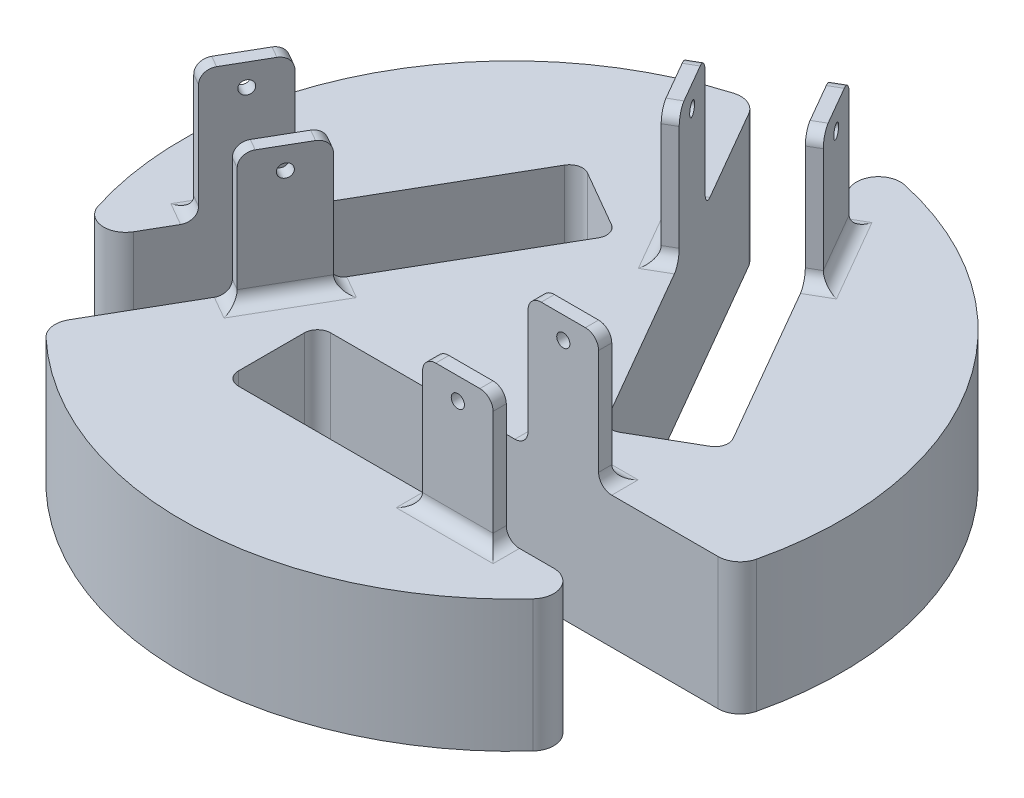
SolidWorks part; units mm, degrees
material "ABS"
ref_plane "Front Plane" through (0, 0, 0) normal (0, 0, 1) x (1, 0, 0)
ref_plane "Top Plane" through (0, 0, 0) normal (0, 1, 0) x (1, 0, 0)
ref_plane "Right Plane" through (0, 0, 0) normal (1, 0, 0) x (0, 0, -1)
sketch "Sketch1" plane through (0, 0, 0) normal (0, 1, 0) x (1, 0, 0)
  circle A0 centre (0, 0) radius 75
  dimension "D1" = 150
extrude "Boss-Extrude1" add sketch "Sketch1" along normal blind 30
sketch "Sketch2" plane through (0, 30, 0) normal (0, 1, 0) x (1, 0, 0)
  line L0 (0, 63.3881) -> (-54.8957, -31.694) construction
  line L1 (-54.8957, -31.694) -> (54.8957, -31.694) construction
  line L2 (54.8957, -31.694) -> (0, 63.3881) construction
  line L3 (0, 63.3881) -> (0, -31.694) construction
  line L4 (-54.8957, -31.694) -> (27.4478, 15.847) construction
  line L5 (54.8957, -31.694) -> (-27.4478, 15.847) construction
  line L6 (3.3338, 30.6137) -> (26.7165, 44.1137)
  line L7 (40.8957, -45.194) -> (24.8454, -45.194)
  line L8 (40.8957, -45.194) -> (40.8957, -18.194)
  line L9 (40.8957, -18.194) -> (24.8454, -18.194)
  line L10 (24.8454, -45.194) -> (24.8454, -18.194)
  line L11 (40.8957, -45.194) -> (24.8454, -18.194) construction
  line L12 (40.8957, -18.194) -> (24.8454, -45.194) construction
  line L13 (-59.587, -12.8197) -> (-36.2044, -26.3197)
  line L14 (-59.587, -12.8197) -> (-51.5619, 1.0803)
  line L15 (-51.5619, 1.0803) -> (-28.1792, -12.4197)
  line L16 (-36.2044, -26.3197) -> (-28.1792, -12.4197)
  line L17 (-59.587, -12.8197) -> (-28.1792, -12.4197) construction
  line L18 (-51.5619, 1.0803) -> (-36.2044, -26.3197) construction
  line L19 (3.3338, 30.6137) -> (-4.6913, 44.5137)
  line L20 (-4.6913, 44.5137) -> (18.6913, 58.0137)
  line L21 (26.7165, 44.1137) -> (18.6913, 58.0137)
  line L22 (3.3338, 30.6137) -> (18.6913, 58.0137) construction
  line L23 (-4.6913, 44.5137) -> (26.7165, 44.1137) construction
  line L24 (-55.5745, -5.8697) -> (-32.1918, -19.3697) construction
  line L25 (32.8705, -18.194) -> (32.8705, -45.194) construction
  line L26 (-32.1918, -19.3697) -> (32.8705, -45.194) construction
  line L27 (22.7039, 51.0637) -> (-0.6788, 37.5637) construction
  line L28 (-0.6788, 37.5637) -> (-55.5745, -5.8697) construction
  line L29 (32.8705, -18.194) -> (22.7039, 51.0637) construction
  point P3 (0, 0)
  point P7 (-43.8831, -12.6197)
  point P10 (32.8705, -31.694)
  point P18 (11.0126, 44.3137)
  dimension "D1" = 14
  dimension "D2" = 27
  dimension "D3" = 27
  dimension "D4" = 27
  dimension "D5" = 70
  dimension "D6" = 14
  dimension "D7" = 14
  dimension "D8" = 70
  dimension "D9" = 70
  dimension "D10" = 95.0821
extrude "Boss-Extrude3" add sketch "Sketch2" along normal blind 30
ref_plane "Plane1" through (24.8454, 30, 18.194) normal (0, 0, 1) x (1, 0, 0)
sketch "Sketch3" plane through (24.8454, 30, 18.194) normal (0, 0, 1) x (1, 0, 0)
  line L0 (16.0503, 25) -> (0, 25) construction
  line L1 (16.0503, 30) -> (16.0503, 0) construction
  line L2 (0, 30) -> (0, 0) construction
  line L3 (8.0252, 25) -> (8.0252, 30) construction
  line L4 (16.0503, 30) -> (0, 30) construction
  circle A0 centre (8.0252, 25) radius 1.5
  dimension "D1" = 3
  dimension "D2" = 5
extrude "Cut-Extrude3" cut sketch "Sketch3" against normal through all both and the other way through all
sketch "Sketch4" plane through (-39.1392, 0, -22.597) normal (-0.866, 0, -0.5) x (-0.5, 0, 0.866)
  line L0 (24.8454, 55) -> (40.8957, 55) construction
  line L2 (40.8957, 60) -> (40.8957, 30) construction
  line L4 (32.8705, 55) -> (32.8705, 60) construction
  line L5 (24.8454, 60) -> (40.8957, 60) construction
  circle A0 centre (32.8705, 55) radius 1.5
  point P9 (24.8454, 55)
  point P10 (40.8957, 55)
  dimension "D1" = 3
  dimension "D2" = 5
extrude "Cut-Extrude4" cut sketch "Sketch4" against normal through all
sketch "Sketch6" plane through (39.1392, 0, -22.597) normal (0.866, 0, -0.5) x (-0.5, 0, -0.866)
  line L0 (24.8454, 55) -> (40.8957, 55) construction
  line L1 (24.8454, 60) -> (24.8454, 30) construction
  line L2 (40.8957, 60) -> (40.8957, 30) construction
  line L3 (32.8705, 55) -> (32.8705, 60) construction
  line L4 (24.8454, 60) -> (40.8957, 60) construction
  circle A0 centre (32.8705, 55) radius 1.5
  dimension "D1" = 3
  dimension "D2" = 5
extrude "Cut-Extrude5" cut sketch "Sketch6" against normal through all
sketch "Sketch7" plane through (0, 60, 0) normal (0, 1, 0) x (1, 0, 0)
  line L0 (40.8957, -42.194) -> (40.8957, -21.194)
  line L1 (40.8957, -42.194) -> (24.845, -42.194)
  line L2 (40.8957, -21.194) -> (24.845, -21.194)
  line L3 (24.845, -42.194) -> (24.845, -21.194)
  line L4 (40.8957, -45.194) -> (40.8957, -18.194) construction
  line L5 (32.8703, -42.194) -> (32.8705, -45.194) construction
  line L8 (24.8454, -45.194) -> (40.8957, -45.194) construction
  line L9 (32.8703, -21.194) -> (32.8705, -18.194) construction
  line L10 (40.8957, -18.194) -> (24.8454, -18.194) construction
  dimension "D1" = 21
  dimension "D2" = 3
  dimension "D3" = 3
extrude "Cut-Extrude6" cut sketch "Sketch7" against normal blind 24
sketch "Sketch8" plane through (0, 60, 0) normal (0, 1, 0) x (1, 0, 0)
  line L0 (-30.7773, -10.9197) -> (-48.9638, -0.4197)
  line L1 (-30.7773, -10.9197) -> (-38.8024, -24.8197)
  line L2 (-48.9638, -0.4197) -> (-56.989, -14.3197)
  line L3 (-38.8024, -24.8197) -> (-56.989, -14.3197)
  line L4 (-28.1792, -12.4197) -> (-51.5619, 1.0803) construction
  line L6 (-59.587, -12.8197) -> (-36.2044, -26.3197) construction
  line L7 (-34.7898, -17.8697) -> (-32.1918, -19.3697) construction
  line L8 (-36.2044, -26.3197) -> (-28.1792, -12.4197) construction
  line L9 (-52.9764, -7.3697) -> (-55.5745, -5.8697) construction
  line L10 (-51.5619, 1.0803) -> (-59.587, -12.8197) construction
  dimension "D1" = 21
extrude "Cut-Extrude7" cut sketch "Sketch8" against normal blind 24
sketch "Sketch9" plane through (0, 60, 0) normal (0, 1, 0) x (1, 0, 0)
  line L0 (16.0933, 56.5137) -> (24.1184, 42.6137)
  line L1 (16.0933, 56.5137) -> (-2.0933, 46.0137)
  line L2 (24.1184, 42.6137) -> (5.9319, 32.1137)
  line L3 (-2.0933, 46.0137) -> (5.9319, 32.1137)
  line L4 (18.6913, 58.0137) -> (-4.6913, 44.5137) construction
  line L5 (3.3338, 30.6137) -> (26.7165, 44.1137) construction
  line L6 (1.9193, 39.0637) -> (-0.6788, 37.5637) construction
  line L7 (-4.6913, 44.5137) -> (3.3338, 30.6137) construction
  line L8 (20.1059, 49.5637) -> (22.7039, 51.0637) construction
  line L9 (26.7165, 44.1137) -> (18.6913, 58.0137) construction
  dimension "D1" = 21
extrude "Cut-Extrude8" cut sketch "Sketch9" against normal blind 24
fillet "Fillet4" radius 3 12 edges at (-0.6788, 30, -37.5637) (15.0252, 30, -37.3637) (7, 30, -51.2637) (22.7039, 30, -51.0637) (32.8705, 30, 18.194) (40.8957, 30, 31.694) (32.8705, 30, 45.194) (24.8454, 30, 31.694) (-32.1918, 30, 19.3697) (-47.8957, 30, 19.5697) (-39.8705, 30, 5.6697) (-55.5745, 30, 5.8697)
sketch "Sketch10" plane through (0, 36, 0) normal (0, 1, 0) x (1, 0, 0)
  line L0 (-25.0127, 41.0649) -> (-6.8261, 30.5649)
  line L1 (-25.0127, 41.0649) -> (-72.5127, -41.2075)
  line L2 (-6.8261, 30.5649) -> (-54.3261, -51.7075)
  line L3 (-72.5127, -41.2075) -> (-54.3261, -51.7075)
  line L4 (-48.9638, -0.4197) -> (-56.989, -14.3197) construction
  line L5 (-38.8024, -24.8197) -> (-30.7773, -10.9197) construction
  circle A0 centre (0, 0) radius 75 construction
  point P8 (0, 0)
  dimension "D1" = 95
extrude "Cut-Extrude9" cut sketch "Sketch10" against normal through all both and the other way through all
sketch "Sketch11" plane through (0, 36, 0) normal (0, 1, 0) x (1, 0, 0)
  line L0 (-17.617, 72.9016) -> (0.5696, 83.4016)
  line L1 (-17.617, 72.9016) -> (29.883, -9.3708)
  line L2 (0.5696, 83.4016) -> (48.0696, 1.1292)
  line L3 (29.883, -9.3708) -> (48.0696, 1.1292)
  line L4 (-2.0933, 46.0137) -> (5.9319, 32.1137) construction
  line L5 (24.1184, 42.6137) -> (16.0933, 56.5137) construction
  arc A0 (-54.3261, -51.7075) -> (-67.5438, -32.6012) centre (0, 0) ccw construction
  point P8 (0, 0)
  dimension "D1" = 95
extrude "Cut-Extrude10" cut sketch "Sketch11" against normal through all both and the other way through all
sketch "Sketch12" plane through (0, 36, 0) normal (0, 1, 0) x (1, 0, 0)
  line L0 (71.9431, -42.194) -> (71.9431, -21.194)
  line L1 (71.9431, -42.194) -> (-23.0569, -42.194)
  line L2 (71.9431, -21.194) -> (-23.0569, -21.194)
  line L3 (-23.0569, -42.194) -> (-23.0569, -21.194)
  line L4 (24.8454, -42.194) -> (40.8957, -42.194) construction
  line L5 (40.8957, -21.194) -> (24.8454, -21.194) construction
  arc A0 (-54.3261, -51.7075) -> (5.5384, 74.7952) centre (0, 0) ccw construction
  point P8 (0, 0)
  dimension "D1" = 95
extrude "Cut-Extrude11" cut sketch "Sketch12" against normal through all both and the other way through all
fillet "Fillet5" radius 5 6 edges at (-17.617, 15, -72.9016) (5.5384, 15, -74.7952) (62.0053, 15, 42.194) (71.9431, 15, 21.194) (-54.3261, 15, 51.7075) (-67.5438, 15, 32.6012)
fillet "Fillet6" radius 3 6 edges at (48.0696, 15, -1.1292) (-6.8261, 15, -30.5649) (-25.0127, 15, -41.0649) (-23.0569, 15, 21.194) (-23.0569, 15, 42.194) (29.883, 15, 9.3708)
fillet "Fillet7" radius 3 12 edges at (25.4175, 60, -43.3637) (4.6329, 60, -31.3637) (-3.3923, 60, -45.2637) (17.3923, 60, -57.2637) (-37.5034, 60, 25.5697) (-58.288, 60, 13.5697) (-50.2628, 60, -0.3303) (-29.4782, 60, 11.6697) (24.8454, 60, 19.694) (24.8454, 60, 43.694) (40.8957, 60, 19.694) (40.8957, 60, 43.694)
